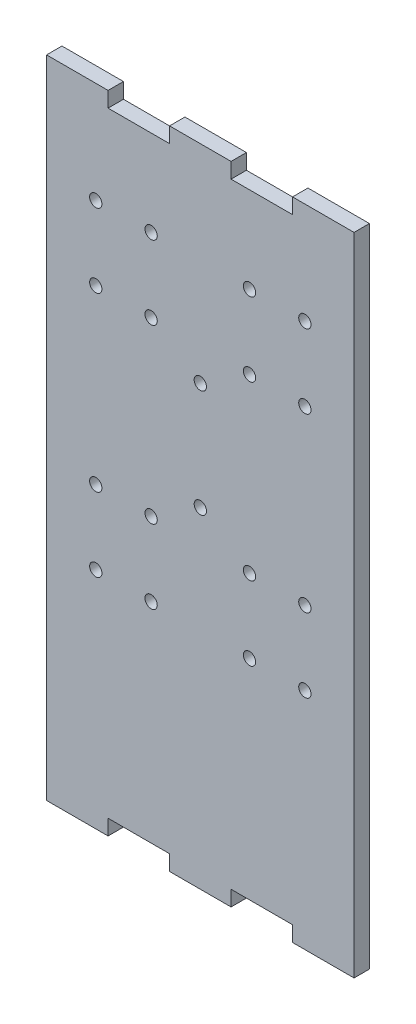
SolidWorks part; units mm, degrees
material "Acrylic (Medium-high impact)"
ref_plane "Front Plane" through (0, 0, 0) normal (0, 0, 1) x (1, 0, 0)
ref_plane "Top Plane" through (0, 0, 0) normal (0, 1, 0) x (1, 0, 0)
ref_plane "Right Plane" through (0, 0, 0) normal (1, 0, 0) x (0, 0, -1)
sketch "Sketch1" plane through (0, 0, 0) normal (0, 0, 1) x (1, 0, 0)
  line L0 (-1739.7044, 0) -> (85245.5138, 0) construction
  line L1 (0, -1739.7044) -> (0, 85245.5138) construction
  line L24 (-50, 85) -> (-50, -125)
  line L26 (50, 85) -> (50, -125)
  line L38 (-50, 85) -> (50, 85)
  line L39 (-50, -125) -> (50, -125)
  point P9 (0, 87.8386)
  dimension "D1" = 100
  dimension "D2" = 50
  dimension "D3" = 85
  dimension "D4" = 125
extrude "Boss-Extrude1" add sketch "Sketch1" along normal blind 5
sketch "Sketch4" plane through (0, 0, 5) normal (0, 0, 1) x (1, 0, 0)
  line L0 (0, 85) -> (0, -130.7623) construction
  line L1 (50, 85) -> (-50, 85) construction
  line L2 (61.8606, 0) -> (-67.3231, 0) construction
  line L3 (-30, 80) -> (-20, 85) construction
  line L8 (10, -120) -> (10, -125)
  line L9 (-10, -120) -> (-10, -125)
  line L11 (30, 85) -> (30, 80)
  line L12 (30, 80) -> (10, 80)
  line L13 (10, 85) -> (10, 80)
  line L14 (20, 85) -> (10, 80) construction
  line L15 (30, 80) -> (20, 85) construction
  line L16 (-20, 85) -> (-10, 80) construction
  line L17 (-30, 80) -> (-10, 80)
  line L18 (-10, 85) -> (-10, 80)
  line L20 (-30, 85) -> (-30, 80)
  line L21 (-30, 85) -> (-10, 85)
  line L22 (-10, 85) -> (10, 85)
  line L23 (10, 85) -> (30, 85)
  line L24 (30, -125) -> (10, -125)
  line L25 (-30, -120) -> (-30, -125)
  line L26 (-30, -125) -> (-10, -125)
  line L27 (10, -120) -> (30, -120)
  line L28 (30, -120) -> (30, -125)
  line L29 (-30, -120) -> (-10, -120)
  point P11 (20, 85)
  point P25 (0, 85)
  line M21 (50, 85) -> (-50, 85)
  dimension "D2" = 20
  dimension "D3" = 5
extrude "Cut-Extrude3" cut sketch "Sketch4" against normal blind 10 contours L20 L17 L18 M21 | L23 L11 L12 L13 | L27 L28 L24 L8 | L29 L9 L26 L25
sketch "Sketch5" plane through (0, 0, 5) normal (0, 0, 1) x (1, 0, 0)
  line L0 (0, 99.2017) -> (0, -143.0536) construction
  line L1 (-82.8198, 0) -> (68.7144, 0) construction
  circle A0 centre (34, 52) radius 2
  circle A1 centre (16, 52) radius 2
  circle A2 centre (16, 28) radius 2
  circle A3 centre (34, 28) radius 2
  circle A4 centre (-16, 28) radius 2
  circle A5 centre (-34, 28) radius 2
  circle A6 centre (-34, 52) radius 2
  circle A7 centre (-16, 52) radius 2
  circle A8 centre (-16, -52) radius 2
  circle A9 centre (-34, -52) radius 2
  circle A10 centre (-34, -28) radius 2
  circle A11 centre (-16, -28) radius 2
  circle A12 centre (16, -28) radius 2
  circle A13 centre (34, -28) radius 2
  circle A14 centre (34, -52) radius 2
  circle A15 centre (16, -52) radius 2
  dimension "D1" = 4
  dimension "D2" = 18
  dimension "D7" = 4
  dimension "D3" = 52
  dimension "D4" = 24
  dimension "D5" = 16
  dimension "D6" = 28
extrude "Cut-Extrude4" cut sketch "Sketch5" against normal through all
sketch "Sketch7" plane through (0, 0, 5) normal (0, 0, 1) x (1, 0, 0)
  line L0 (0, -1000) -> (50000, -1000) construction
  line L1 (-1000, 0) -> (49000, 0) construction
  line L2 (0, -1000) -> (0, 49000) construction
  circle A0 centre (0, 17.5) radius 2
  circle A1 centre (0, -17.5) radius 2
  dimension "D1" = 4
  dimension "D2" = 4
  dimension "D3" = 17.5
  dimension "D4" = 35
extrude "Cut-Extrude5" cut sketch "Sketch7" against normal blind 10
